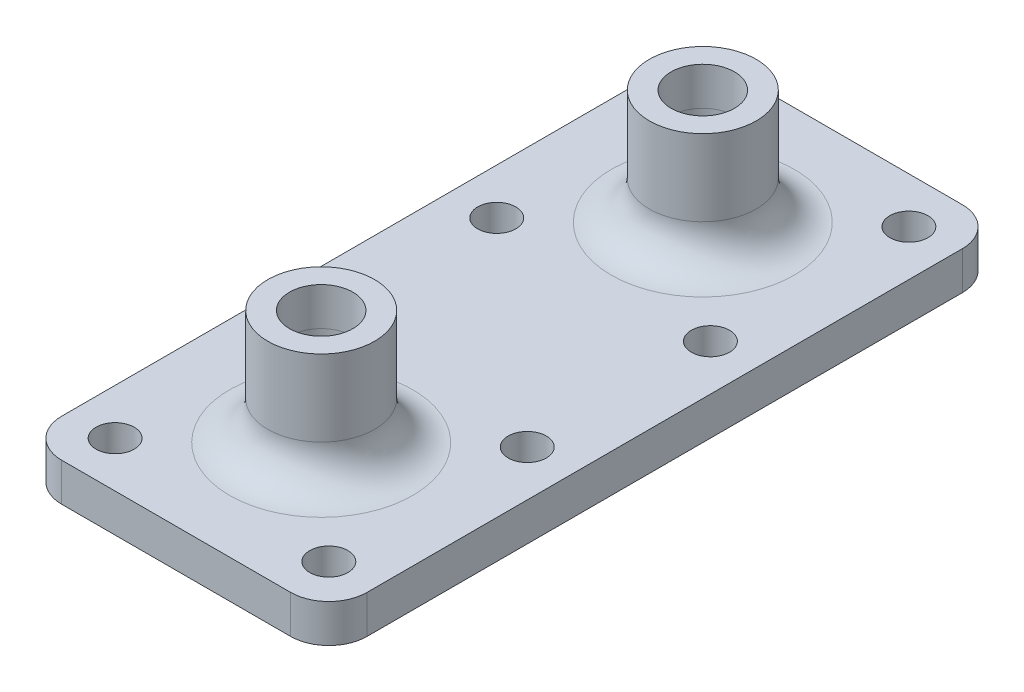
SolidWorks part; units mm, degrees
ref_plane "Front Plane" through (0, 0, 0) normal (0, 0, 1) x (1, 0, 0)
ref_plane "Top Plane" through (0, 0, 0) normal (0, 1, 0) x (1, 0, 0)
ref_plane "Right Plane" through (0, 0, 0) normal (1, 0, 0) x (0, 0, -1)
sketch "Sketch1" plane through (0, 0, 0) normal (0, 1, 0) x (1, 0, 0)
  line L0 (0, 44) -> (0, -44) construction
  line L13 (20, -44) -> (-20, -44)
  line L14 (20, -44) -> (20, 44)
  line L15 (20, 44) -> (-20, 44)
  line L16 (-20, -44) -> (-20, 44)
  line L17 (20, -44) -> (-20, 44) construction
  line L18 (20, 44) -> (-20, -44) construction
  line L19 (-1000, 0) -> (49000, 0) construction
  line L20 (14, 12) -> (-14, 12) construction
  line L21 (14, 12) -> (14, 38) construction
  line L22 (14, 38) -> (-14, 38) construction
  line L23 (-14, 12) -> (-14, 38) construction
  line L24 (14, 12) -> (-14, 38) construction
  line L25 (14, 38) -> (-14, 12) construction
  line L26 (-14, -12) -> (14, -12) construction
  line L27 (-14, -12) -> (-14, -38) construction
  line L28 (-14, -38) -> (14, -38) construction
  line L29 (14, -12) -> (14, -38) construction
  line L30 (-14, -12) -> (14, -38) construction
  line L31 (-14, -38) -> (14, -12) construction
  circle A4 centre (-14, 38) radius 2.5
  circle A5 centre (14, 38) radius 2.5
  circle A6 centre (-14, 12) radius 2.5
  circle A7 centre (14, 12) radius 2.5
  circle A8 centre (-14, -12) radius 2.5
  circle A9 centre (-14, -38) radius 2.5
  circle A10 centre (14, -38) radius 2.5
  circle A11 centre (14, -12) radius 2.5
  point P0 (0, 0)
  point P17 (0, 25)
  point P27 (0, -25)
  dimension "D10" = 5
  dimension "D6" = 28
  dimension "D7" = 6
  dimension "D8" = 6
  dimension "D9" = 50
  dimension "D11" = 26
extrude "Boss-Extrude1" add sketch "Sketch1" along normal blind 5
sketch "Sketch2" plane through (0, 0, 0) normal (0, 1, 0) x (1, 0, 0)
  line L0 (0, 25) -> (0, -25) construction
  circle A0 centre (0, 25) radius 4.15
  circle A1 centre (0, -25) radius 4.15
  circle A2 centre (0, 25) radius 7
  circle A3 centre (0, -25) radius 7
  point P4 (0, 0)
  point P8 (78.3235, 32.8296)
  dimension "D1" = 50
  dimension "D2" = 8.3
  dimension "D3" = 14
extrude "Boss-Extrude2" add sketch "Sketch2" along normal blind 20
chamfer "Chamfer1" distance 10 angle 1 2 edges at (0, 5, -20.85) (0, 5, 29.15)
fillet "Fillet1" radius 5 6 edges at (20, 2.5, -44) (-20, 2.5, -44) (-20, 2.5, 44) (20, 2.5, 44) (0, 5, 32) (0, 5, -18)
